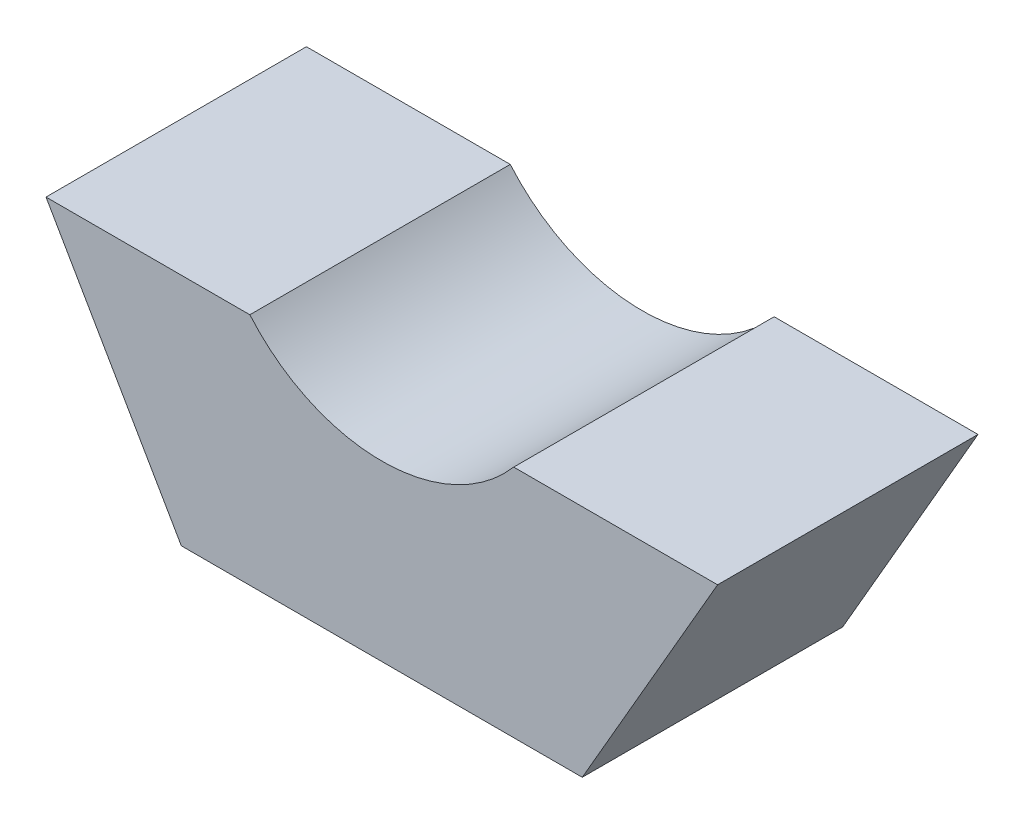
SolidWorks part; units mm, degrees
ref_plane "정면" through (0, 0, 0) normal (0, 0, 1) x (1, 0, 0)
ref_plane "윗면" through (0, 0, 0) normal (0, 1, 0) x (1, 0, 0)
ref_plane "우측면" through (0, 0, 0) normal (1, 0, 0) x (0, 0, -1)
sketch "스케치1" plane through (0, 0, 0) normal (0, 0, 1) x (1, 0, 0)
  line L1 (46.188, 0) -> (23.094, 40)
  line L2 (23.094, 40) -> (-23.094, 40)
  line L3 (-23.094, 40) -> (-46.188, 0)
  line L4 (-46.188, 0) -> (-23.094, -40)
  line L5 (-23.094, -40) -> (23.094, -40)
  line L6 (23.094, -40) -> (46.188, 0)
  circle A0 centre (0, 0) radius 40 construction
  circle A1 centre (0, 0) radius 20
extrude "보스-돌출1" add sketch "스케치1" along normal blind 30
sketch "스케치2" plane through (0, 0, 0) normal (0, 0, 1) x (1, 0, 0)
  line L1 (-50.6766, 0) -> (52.0577, 0)
  line L2 (-50.6766, 0) -> (-50.6766, 41.1681)
  line L3 (-50.6766, 41.1681) -> (52.0577, 41.1681)
  line L4 (52.0577, 0) -> (52.0577, 41.1681)
extrude "컷-돌출1" cut sketch "스케치2" along normal blind 89
sketch "스케치3" plane through (0, 0, 30) normal (0, 0, 1) x (1, 0, 0)
  line L1 (46.188, 0) -> (-46.7338, 0)
  line L2 (46.188, 0) -> (46.188, -3)
  line L3 (46.188, -3) -> (-46.7338, -3)
  line L4 (-46.7338, 0) -> (-46.7338, -3)
  dimension "D1" = 3
extrude "컷-돌출2" cut sketch "스케치3" against normal blind 89
sketch "스케치5" plane through (0, 0, 30) normal (0, 0, 1) x (1, 0, 0)
  line L1 (44.456, -3) -> (-44.7988, -3)
  line L2 (44.456, -3) -> (44.456, -13)
  line L3 (44.456, -13) -> (-44.7988, -13)
  line L4 (-44.7988, -3) -> (-44.7988, -13)
  dimension "D1" = 10
extrude "컷-돌출3" cut sketch "스케치5" against normal through all
